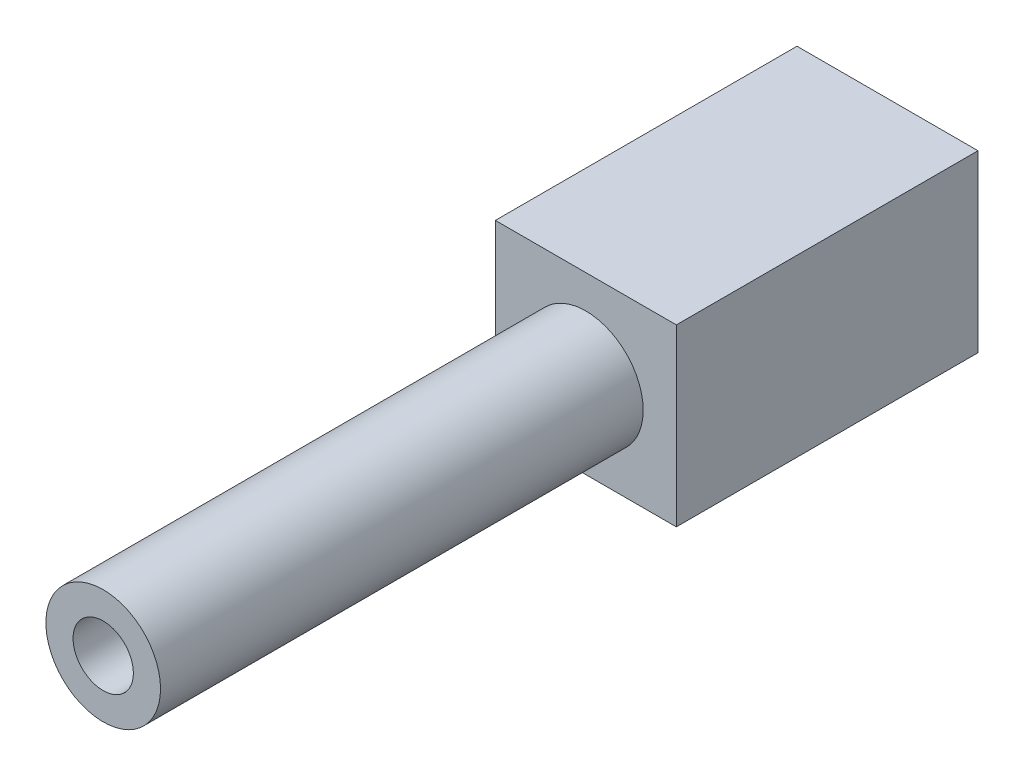
SolidWorks part; units mm, degrees
ref_plane "Спереди" through (0, 0, 0) normal (0, 0, 1) x (1, 0, 0)
ref_plane "Сверху" through (0, 0, 0) normal (0, 1, 0) x (1, 0, 0)
ref_plane "Справа" through (0, 0, 0) normal (1, 0, 0) x (0, 0, -1)
sketch "Эскиз1" plane through (0, 0, 0) normal (0, 0, 1) x (1, 0, 0)
  circle A0 centre (0, 0) radius 1.9
  circle A1 centre (0, 0) radius 1
  dimension "D1" = 3.8
  dimension "D2" = 2
extrude "Бобышка-Вытянуть1" add sketch "Эскиз1" along normal blind 16 contours A1
sketch "Эскиз2" plane through (0, 0, 0) normal (0, 0, 1) x (1, 0, 0)
  line L2 (-3, 3) -> (3, 3)
  line L3 (-3, 3) -> (-3, -2.8)
  line L4 (-3, -2.8) -> (3, -2.8)
  line L5 (3, 3) -> (3, -2.8)
  dimension "D1" = 3
  dimension "D2" = 3
  dimension "D3" = 2.8
  dimension "D4" = 3
extrude "Бобышка-Вытянуть2" add sketch "Эскиз2" against normal blind 10
